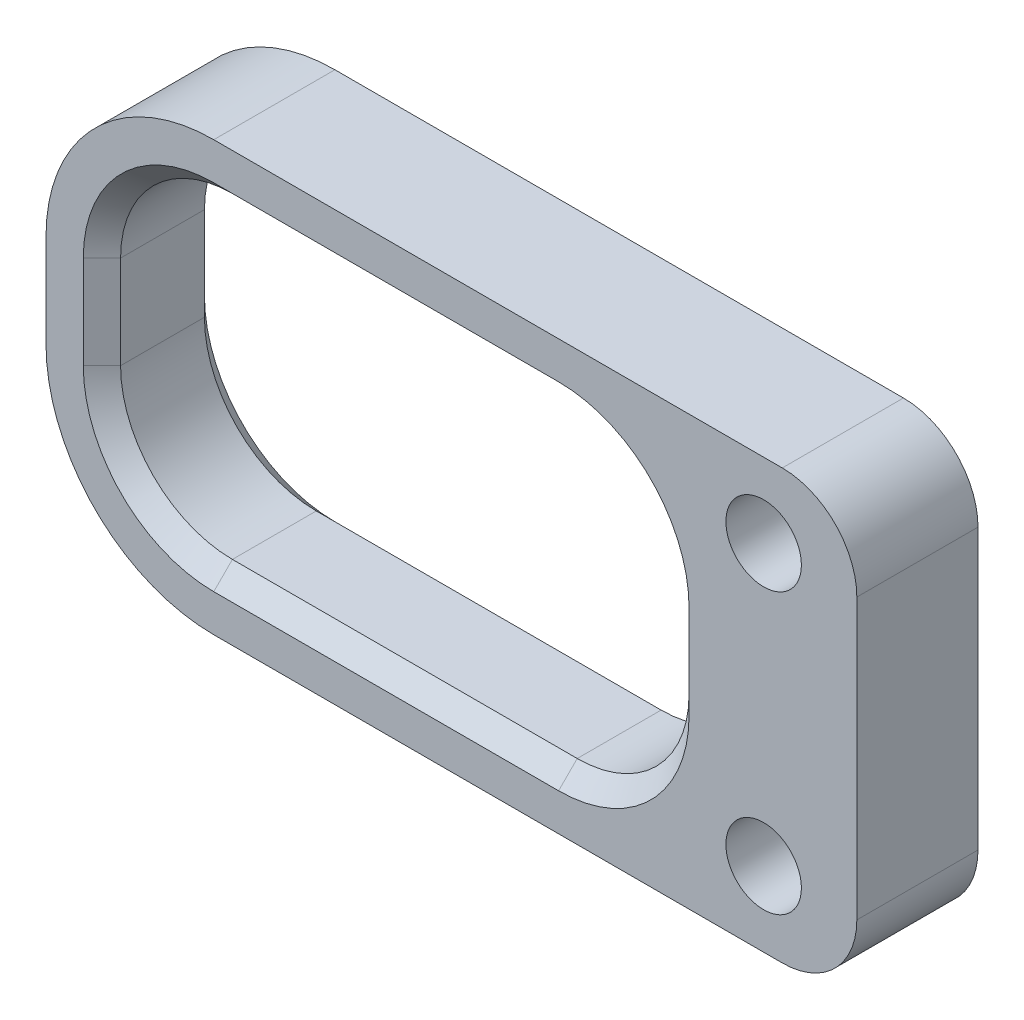
SolidWorks part; units mm, degrees
ref_plane "Front Plane" through (0, 0, 0) normal (0, 0, 1) x (1, 0, 0)
ref_plane "Top Plane" through (0, 0, 0) normal (0, 1, 0) x (1, 0, 0)
ref_plane "Right Plane" through (0, 0, 0) normal (1, 0, 0) x (0, 0, -1)
sketch "Sketch1" plane through (0, 0, 0) normal (0, 0, 1) x (1, 0, 0)
  line L1 (-29.5, 4) -> (1, 4)
  line L2 (-38.5, -5) -> (-38.5, -10)
  line L3 (-29.5, -19) -> (1, -19)
  line L4 (5, 0) -> (5, -15)
  line L5 (0, 0) -> (0, -15) construction
  line L6 (-29.5, 1) -> (-11, 1)
  line L7 (0, -7.5) -> (5, -7.5) construction
  line L8 (-35.5, -5) -> (-35.5, -10)
  line L9 (-29.5, -16) -> (-11, -16)
  line L10 (-5, -5) -> (-5, -10)
  circle A0 centre (0, 0) radius 2.0255
  circle A1 centre (0, -15) radius 2.0255
  arc A2 (-29.5, 4) -> (-38.5, -5) centre (-29.5, -5) ccw
  arc A3 (1, -19) -> (5, -15) centre (1, -15) ccw
  arc A4 (1, 4) -> (5, 0) centre (1, 0) cw
  arc A5 (-38.5, -10) -> (-29.5, -19) centre (-29.5, -10) ccw
  arc A6 (-11, 1) -> (-5, -5) centre (-11, -5) cw
  arc A7 (-11, -16) -> (-5, -10) centre (-11, -10) ccw
  arc A8 (-35.5, -10) -> (-29.5, -16) centre (-29.5, -10) ccw
  arc A9 (-29.5, 1) -> (-35.5, -5) centre (-29.5, -5) ccw
  point P12 (-38.5, 4)
  point P16 (5, -19)
  point P19 (5, 4)
  dimension "D2" = 4.051
  dimension "D5" = 9
  dimension "D8" = 4
  dimension "D7" = 6
  dimension "D1" = 15
  dimension "D3" = 23
  dimension "D4" = 5
  dimension "D6" = 43.5
  dimension "D9" = 3
  dimension "D10" = 3
  dimension "D11" = 3
  dimension "D12" = 5
extrude "Boss-Extrude1" add sketch "Sketch1" along normal blind 6.5
chamfer "Chamfer1" distance 1 angle 45 16 edges at (-20.25, 1, 0) (-33.7426, -0.7574, 0) (-6.7574, -0.7574, 0) (-35.5, -7.5, 0) (-5, -7.5, 0) (-33.7426, -14.2426, 0) (-6.7574, -14.2426, 0) (-20.25, -16, 0) (-20.25, -16, 6.5) (-6.7574, -14.2426, 6.5) (-33.7426, -14.2426, 6.5) (-5, -7.5, 6.5) (-35.5, -7.5, 6.5) (-6.7574, -0.7574, 6.5) (-33.7426, -0.7574, 6.5) (-20.25, 1, 6.5)
